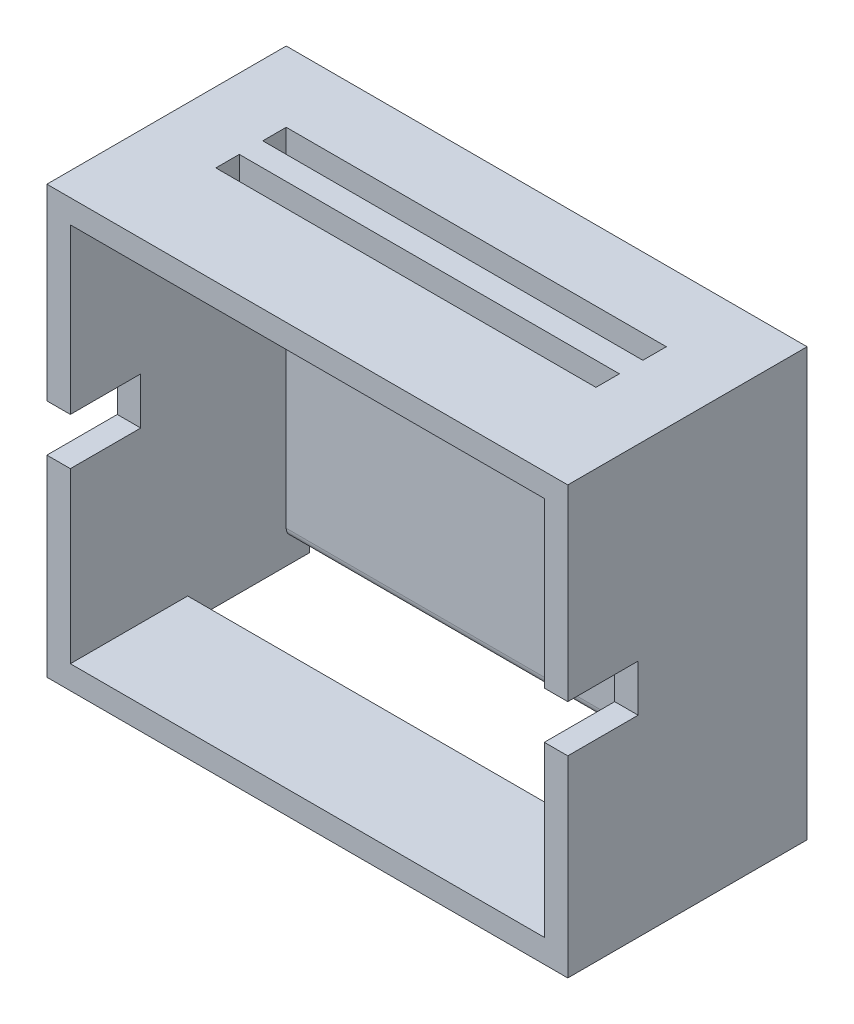
SolidWorks part; units mm, degrees
ref_plane "前基準面" through (0, 0, 0) normal (0, 0, 1) x (1, 0, 0)
ref_plane "上基準面" through (0, 0, 0) normal (0, 1, 0) x (1, 0, 0)
ref_plane "右基準面" through (0, 0, 0) normal (1, 0, 0) x (0, 0, -1)
sketch "草圖1" plane through (0, 0, 0) normal (0, 0, 1) x (1, 0, 0)
  line L1 (-32.1089, 46.7555) -> (68.8911, 46.7555)
  line L2 (-32.1089, 46.7555) -> (-32.1089, -34.2445)
  line L3 (-32.1089, -34.2445) -> (68.8911, -34.2445)
  line L4 (68.8911, 46.7555) -> (68.8911, -34.2445)
  line L5 (-37.1089, 51.7555) -> (73.8911, 51.7555)
  line L6 (-37.1089, 51.7555) -> (-37.1089, -39.2445)
  line L7 (-37.1089, -39.2445) -> (73.8911, -39.2445)
  line L8 (73.8911, 51.7555) -> (73.8911, -39.2445)
  dimension "D1" = 81
  dimension "D2" = 101
  dimension "D3" = 5
  dimension "D4" = 5
  dimension "D5" = 5
  dimension "D6" = 5
extrude "填料-伸長1" add sketch "草圖1" along normal blind 46
sketch "草圖2" plane through (0, 0, 0) normal (0, 0, -1) x (-1, 0, 0)
  line L1 (37.1089, -39.2445) -> (-73.8911, -39.2445)
  line L2 (37.1089, -39.2445) -> (37.1089, 51.7555)
  line L3 (37.1089, 51.7555) -> (-73.8911, 51.7555)
  line L4 (-73.8911, -39.2445) -> (-73.8911, 51.7555)
extrude "填料-伸長2" add sketch "草圖2" along normal blind 5
sketch "草圖3" plane through (0, -39.2445, 0) normal (0, -1, 0) x (1, 0, 0)
  line L0 (-37.1089, 46) -> (-37.1089, -5) construction
  line L1 (-32.1089, 21) -> (68.8911, 21)
  line L2 (-32.1089, 21) -> (-32.1089, -5)
  line L3 (-32.1089, -5) -> (68.8911, -5)
  line L4 (68.8911, 21) -> (68.8911, -5)
  line L5 (73.8911, 46) -> (73.8911, -5) construction
  dimension "D1" = 5
  dimension "D2" = 5
  dimension "D3" = 26
extrude "除料-伸長1" cut sketch "草圖3" against normal blind 5
fillet "圓角1" radius 2 1 edges at (18.3911, -34.2445, 0)
sketch "草圖4" plane through (0, 0, 46) normal (0, 0, 1) x (1, 0, 0)
  line L0 (-37.1089, 51.7555) -> (-37.1089, -39.2445) construction
  line L1 (-37.1089, 11.7555) -> (-32.1089, 11.7555)
  line L2 (-37.1089, 11.7555) -> (-37.1089, 1.7555)
  line L3 (-37.1089, 1.7555) -> (-32.1089, 1.7555)
  line L4 (-32.1089, 11.7555) -> (-32.1089, 1.7555)
  line L5 (-32.1089, 46.7555) -> (-32.1089, -34.2445) construction
  line L6 (68.8911, -34.2445) -> (68.8911, 46.7555) construction
  line L7 (68.8911, 11.7555) -> (73.8911, 11.7555)
  line L8 (68.8911, 11.7555) -> (68.8911, 1.7555)
  line L9 (68.8911, 1.7555) -> (73.8911, 1.7555)
  line L10 (73.8911, 11.7555) -> (73.8911, 1.7555)
  line L11 (73.8911, -39.2445) -> (73.8911, 51.7555) construction
  line L12 (73.8911, 51.7555) -> (-37.1089, 51.7555) construction
  dimension "D1" = 40
  dimension "D2" = 40
  dimension "D3" = 10
  dimension "D4" = 10
extrude "除料-伸長2" cut sketch "草圖4" against normal blind 15
sketch "草圖5" plane through (0, 51.7555, 0) normal (0, 1, 0) x (1, 0, 0)
  line L0 (-37.1089, 5) -> (73.8911, 5) construction
  line L1 (58.8911, -25) -> (-22.1089, -25)
  line L2 (58.8911, -25) -> (58.8911, -20)
  line L3 (58.8911, -20) -> (-22.1089, -20)
  line L4 (-22.1089, -25) -> (-22.1089, -20)
  line L5 (58.8911, -15) -> (-22.1089, -15)
  line L6 (58.8911, -15) -> (58.8911, -10)
  line L7 (58.8911, -10) -> (-22.1089, -10)
  line L8 (-22.1089, -15) -> (-22.1089, -10)
  line L9 (73.8911, -46) -> (73.8911, 5) construction
  line L10 (-37.1089, -46) -> (-37.1089, 5) construction
  dimension "D1" = 15
  dimension "D2" = 15
  dimension "D3" = 15
  dimension "D4" = 5
  dimension "D5" = 15
  dimension "D6" = 15
  dimension "D7" = 5
  dimension "D8" = 5
extrude "除料-伸長3" cut sketch "草圖5" against normal blind 5
